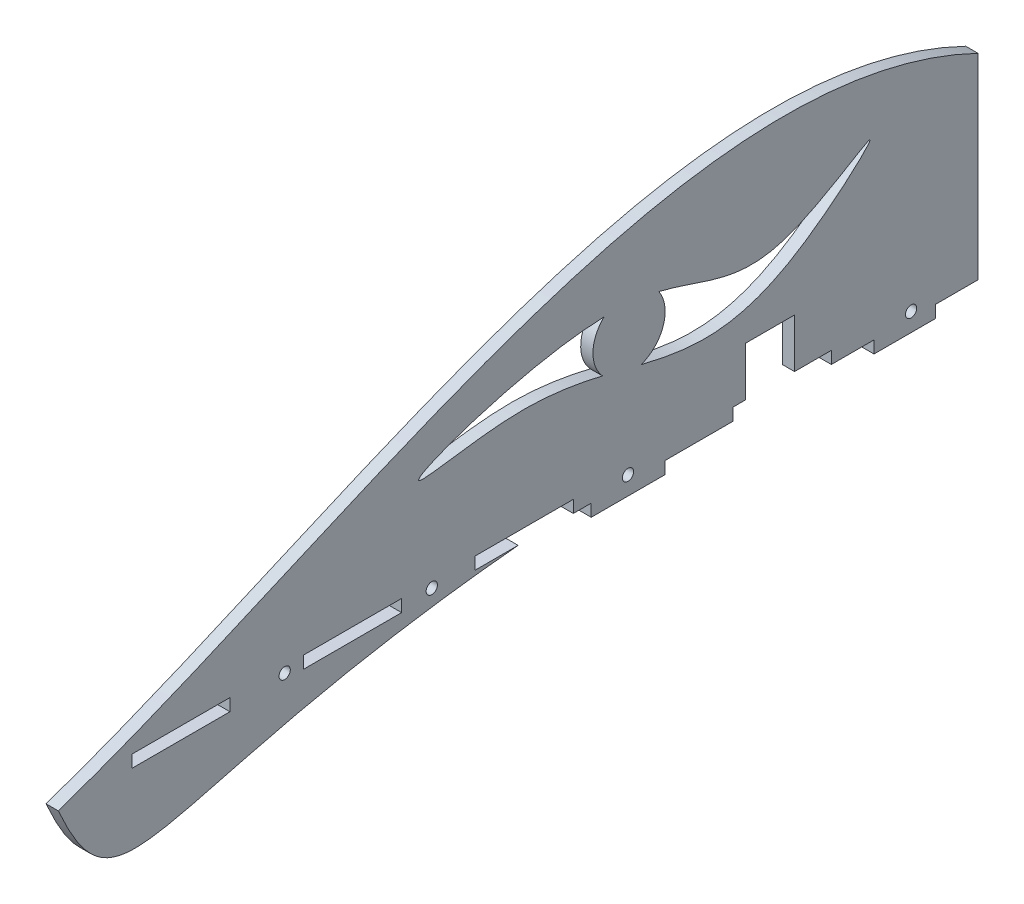
SolidWorks part; units mm, degrees
ref_plane "Front Plane" through (0, 0, 0) normal (0, 0, 1) x (1, 0, 0)
ref_plane "Top Plane" through (0, 0, 0) normal (0, 1, 0) x (1, 0, 0)
ref_plane "Right Plane" through (0, 0, 0) normal (1, 0, 0) x (0, 0, -1)
sketch "Sketch1" plane through (0, 0, 0) normal (1, 0, 0) x (0, 0, -1)
  line L0 (119.0625, 0) -> (238.125, 0)
  line L3 (238.125, 50.8) -> (238.125, 0)
  spline S0 degree 3 poles (0, 0) (76.8598, 26.0709) (164.0748, 86.6237) (238.125, 50.8) knots 0 0 0 0 1 1 1 1
  spline S1 degree 3 poles (0, 0) (16.1049, -36.273) (24.4435, -9.0391) (119.0625, 0) knots 0 0 0 0 1 1 1 1
  dimension "D1" = 238.125
extrude "Boss-Extrude1" add sketch "Sketch1" along normal blind 3.175
sketch "Sketch2" plane through (3.175, 0, 0) normal (1, 0, 0) x (0, 0, -1)
  line L0 (238.125, 0) -> (238.125, 50.8) construction
  line L2 (238.125, 0) -> (238.125, 3.175)
  line L4 (0, 0) -> (0, 3.175)
  line L5 (19.05, 0) -> (44.45, 0)
  line L6 (19.05, 0) -> (19.05, 3.175)
  line L7 (19.05, 3.175) -> (44.45, 3.175)
  line L8 (44.45, 0) -> (44.45, 3.175)
  line L9 (63.5, 0) -> (88.9, 0)
  line L10 (63.5, 0) -> (63.5, 3.175)
  line L11 (63.5, 3.175) -> (88.9, 3.175)
  line L12 (88.9, 0) -> (88.9, 3.175)
  line L13 (107.95, 0) -> (133.35, 0)
  line L14 (107.95, 0) -> (107.95, 3.175)
  line L15 (107.95, 3.175) -> (133.35, 3.175)
  line L16 (133.35, 0) -> (133.35, 3.175)
  line L17 (200.152, 0) -> (174.752, 0)
  line L18 (200.152, 0) -> (200.152, 3.175)
  line L19 (200.152, 3.175) -> (174.752, 3.175)
  line L20 (174.752, 0) -> (174.752, 3.175)
  line L22 (195.707, 3.175) -> (183.007, 3.175)
  line L24 (190.627, 15.875) -> (183.007, 15.875)
  line L26 (190.627, 3.175) -> (177.927, 3.175)
  line L27 (190.627, 3.175) -> (190.627, 15.875)
  line L28 (190.627, 15.875) -> (177.927, 15.875)
  line L29 (177.927, 3.175) -> (177.927, 15.875)
  circle A0 centre (96.7105, 1.5875) radius 1.4605
  circle A1 centre (58.6105, 1.5875) radius 1.4605
  circle A2 centre (147.5105, 1.5875) radius 1.4605
  circle A3 centre (220.7895, 1.5875) radius 1.4605
  dimension "D10" = 2.921
  dimension "D11" = 2.921
  dimension "D12" = 2.921
  dimension "D20" = 2.921
  dimension "D1" = 3.175
  dimension "D2" = 19.05
  dimension "D3" = 25.4
  dimension "D4" = 63.5
  dimension "D5" = 25.4
  dimension "D6" = 107.95
  dimension "D7" = 25.4
  dimension "D8" = 63.373
  dimension "D9" = 25.4
  dimension "D13" = 14.1605
  dimension "D14" = 7.8105
  dimension "D15" = 14.1605
  dimension "D16" = 17.3355
  dimension "D19" = 12.7
  dimension "D21" = 9.525
extrude "Cut-Extrude1" cut sketch "Sketch2" against normal blind 6.35
sketch "Sketch3" plane through (3.175, 0, 0) normal (1, 0, 0) x (0, 0, -1)
  line L0 (133.35, 0) -> (174.752, 0) construction
  line L2 (137.982, -3.175) -> (137.982, 0)
  line L4 (157.032, -3.175) -> (157.032, 0)
  line L5 (137.982, -3.175) -> (157.032, 3.175) construction
  line L6 (137.982, 3.175) -> (157.032, -3.175) construction
  line L7 (200.152, 0) -> (238.125, 0) construction
  line L8 (211.201, -3.175) -> (227.076, -3.175)
  line L9 (211.201, -3.175) -> (211.201, 0)
  line L11 (227.076, -3.175) -> (227.076, 0)
  line L12 (211.201, -3.175) -> (227.076, 3.175) construction
  line L13 (208.0673, 4.4285) -> (227.076, -3.175) construction
  line L16 (137.982, -3.175) -> (157.032, -3.175)
  line L17 (137.982, 0) -> (137.982, 0.0262)
  line L18 (137.982, 0.0262) -> (157.032, 0.0262)
  line L19 (157.032, 0.0262) -> (157.032, 0)
  line L20 (211.201, 0) -> (208.026, 0.0262)
  line L21 (208.026, 0.0262) -> (227.076, 0.0262)
  line L22 (227.076, 0.0262) -> (227.076, 0)
  point P0 (147.507, 0)
  point P7 (219.1385, 0)
  dimension "D1" = 6.35
  dimension "D2" = 19.05
  dimension "D3" = 6.35
  dimension "D4" = 19.05
extrude "Boss-Extrude3" add sketch "Sketch3" against normal blind 3.175
sketch "Sketch4" plane through (3.175, 0, 0) normal (1, 0, 0) x (0, 0, -1)
  spline S0 degree 3 poles (142.4572, 36.659) (71.3473, 21.5572) (153.1865, 52.1295) (177.6114, 22.9406) (221.2341, 54.3809) (168.9079, 6.3872) (142.4572, 36.659) (71.3473, 21.5572) (153.1865, 52.1295) knots -0.502863 -0.398106 -0.10079 0 0.221914 0.399724 0.497137 0.601894 0.89921 1 1.221914 1.399724 1.497137 only from (93.9966, 27.197) to (93.9966, 27.197)
extrude "Cut-Extrude2" cut sketch "Sketch4" against normal blind 3.175
sketch "Sketch5" plane through (3.175, 0, 0) normal (1, 0, 0) x (0, 0, -1)
  circle A0 centre (147.7781, 33.3983) radius 9.3426
extrude "Boss-Extrude4" add sketch "Sketch5" against normal blind 3.175
sketch "Sketch7" plane through (3.175, 0, 0) normal (1, 0, 0) x (0, 0, -1)
  line L0 (0, 14.6359) -> (0, -18.6232)
